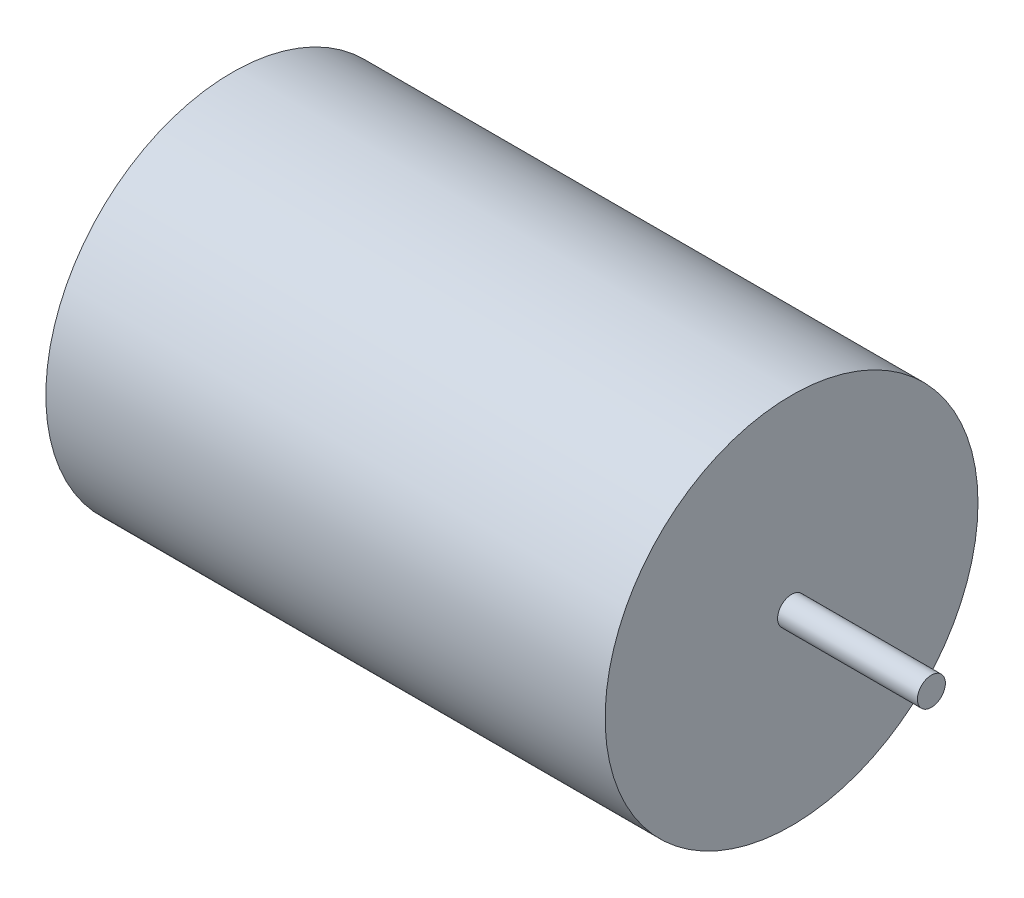
SolidWorks part; units mm, degrees
material "1100-H12 Barre (SS)"
ref_plane "Plan de face" through (0, 0, 0) normal (0, 0, 1) x (1, 0, 0)
ref_plane "Plan de dessus" through (0, 0, 0) normal (0, 1, 0) x (1, 0, 0)
ref_plane "Plan de droite" through (0, 0, 0) normal (1, 0, 0) x (0, 0, -1)
sketch "Esquisse2" plane through (0, 0, 0) normal (1, 0, 0) x (0, 0, -1)
  circle A0 centre (0, 0) radius 20
  dimension "D1" = 40
extrude "Boss.-Extru.1" add sketch "Esquisse2" along normal blind 60
sketch "Esquisse3" plane through (60, 0, 0) normal (1, 0, 0) x (0, 0, -1)
  circle A0 centre (0, 0) radius 1.5
  dimension "D1" = 3
extrude "Boss.-Extru.2" add sketch "Esquisse3" along normal blind 15
